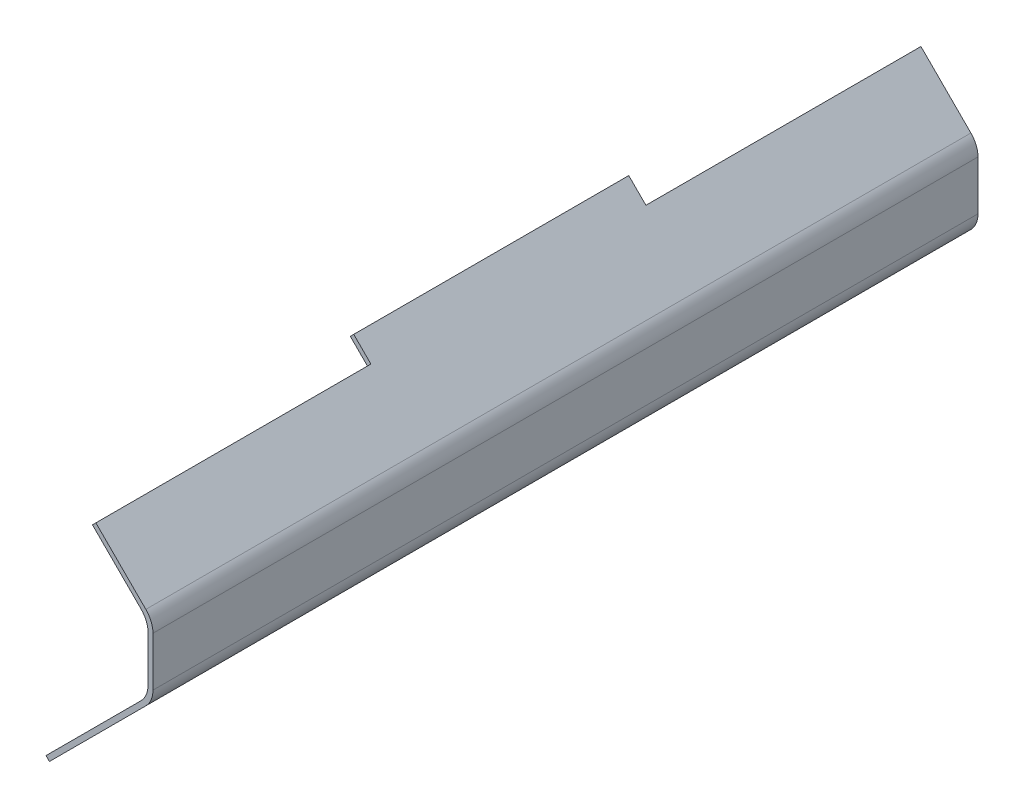
SolidWorks part; units mm, degrees
ref_plane "Front Plane" through (0, 0, 0) normal (0, 0, 1) x (1, 0, 0)
ref_plane "Top Plane" through (0, 0, 0) normal (0, 1, 0) x (1, 0, 0)
ref_plane "Right Plane" through (0, 0, 0) normal (1, 0, 0) x (0, 0, -1)
sketch "Sketch1" plane through (0, 0, 0) normal (0, 0, 1) x (1, 0, 0)
  line L0 (-55.533, 36.3909) -> (-36.3909, 55.533) construction
  line L1 (-36.3909, 55.533) -> (36.3909, 55.533) construction
  line L2 (36.3909, 55.533) -> (55.533, 36.3909) construction
  line L3 (55.533, 36.3909) -> (55.533, -36.3909) construction
  line L4 (55.533, -36.3909) -> (36.3909, -55.533) construction
  line L5 (36.3909, -55.533) -> (-36.3909, -55.533) construction
  line L6 (-36.3909, -55.533) -> (-55.533, -36.3909) construction
  line L7 (-55.533, -36.3909) -> (-55.533, 36.3909) construction
  line L8 (0, 0) -> (0, 31.0491) construction
  line L9 (0, 0) -> (32.6609, 0) construction
  line L10 (-48.4619, 43.4619) -> (-36.3909, 55.533) construction
  line L11 (-45.9619, -45.9619) -> (45.9619, -45.9619) construction
  line L12 (-45.9619, -45.9619) -> (-45.9619, 45.9619) construction
  line L13 (-45.9619, 45.9619) -> (45.9619, 45.9619) construction
  line L14 (45.9619, -45.9619) -> (45.9619, 45.9619) construction
  line L15 (-36.3909, 55.533) -> (-29.3198, 48.4619) construction
  line L16 (-29.3198, 48.4619) -> (43.4619, 48.4619) construction
  line L17 (43.4619, 48.4619) -> (55.533, 36.3909) construction
  line L18 (55.533, 36.3909) -> (48.4619, 29.3198) construction
  line L19 (48.4619, 29.3198) -> (48.4619, -43.4619) construction
  line L20 (48.4619, -43.4619) -> (36.3909, -55.533) construction
  line L21 (36.3909, -55.533) -> (29.3198, -48.4619) construction
  line L22 (29.3198, -48.4619) -> (-43.4619, -48.4619) construction
  line L23 (-43.4619, -48.4619) -> (-55.533, -36.3909) construction
  line L24 (-55.533, -36.3909) -> (-48.4619, -29.3198) construction
  line L25 (-48.4619, -29.3198) -> (-48.4619, 43.4619) construction
  line L26 (36.3909, -55.533) -> (91.9239, 0) construction
  line L27 (91.9239, 0) -> (48.4619, 43.4619) construction
  line L28 (48.4619, 43.4619) -> (49.8762, 44.8762)
  line L29 (49.8762, 44.8762) -> (94.7523, 0) construction
  line L30 (94.7523, 0) -> (37.8051, -56.9472) construction
  line L31 (37.8051, -56.9472) -> (36.3909, -55.533)
  line L32 (78.4619, 13.4619) -> (78.4619, -13.4619)
  line L33 (80.4619, 14.2904) -> (80.4619, -14.2904)
  line L34 (78.4619, 13.4619) -> (48.4619, 43.4619)
  line L35 (49.8762, 44.8762) -> (80.4619, 14.2904)
  line L36 (80.4619, -14.2904) -> (37.8051, -56.9472)
  line L37 (36.3909, -55.533) -> (78.4619, -13.4619)
  point P18 (-45.9619, 45.9619)
  dimension "D1" = 10
  dimension "D2" = 10
  dimension "D3" = 2.5
  dimension "D4" = 2
  dimension "D5" = 2
  dimension "D6" = 2
  dimension "D7" = 30
extrude "Boss-Extrude1" add sketch "Sketch1" along normal blind 340
sketch "Sketch4" plane through (45.9619, 45.9619, 0) normal (-0.7071, -0.7071, 0) x (0, 0, 1)
  line L0 (113.3333, -13.5355) -> (226.6667, -13.5355) construction
  line L1 (0, -3.5355) -> (113.3333, -3.5355)
  line L2 (0, -3.5355) -> (0, -13.5355)
  line L3 (0, -13.5355) -> (113.3333, -13.5355)
  line L4 (113.3333, -3.5355) -> (113.3333, -13.5355)
  line L5 (340, -3.5355) -> (226.6667, -3.5355)
  line L6 (340, -3.5355) -> (340, -13.5355)
  line L7 (340, -13.5355) -> (226.6667, -13.5355)
  line L8 (226.6667, -3.5355) -> (226.6667, -13.5355)
  dimension "D1" = 10
extrude "Cut-Extrude3" cut sketch "Sketch4" against normal through all
sketch "Sketch5" plane through (45.9619, -45.9619, 0) normal (-0.7071, 0.7071, 0) x (0, 0, 1)
  line L0 (340, -13.5355) -> (0, -13.5355) construction
  line L1 (113.3333, -13.5355) -> (226.6667, -13.5355)
  line L2 (113.3333, -13.5355) -> (113.3333, -3.5355)
  line L3 (113.3333, -3.5355) -> (226.6667, -3.5355)
  line L4 (226.6667, -13.5355) -> (226.6667, -3.5355)
  line L5 (113.3333, -3.5355) -> (0, -3.5355) construction
  line L6 (0, 45.9619) -> (0, -13.5355) construction
  line L7 (226.6667, -3.5355) -> (340, -3.5355) construction
  line L8 (340, 45.9619) -> (340, -13.5355) construction
  dimension "D1" = 10
extrude "Cut-Extrude4" cut sketch "Sketch5" against normal through all
fillet "Fillet2" radius 10 4 edges at (80.4619, 14.2904, 170) (80.4619, -14.2904, 170) (78.4619, -13.4619, 170) (78.4619, 13.4619, 170)
